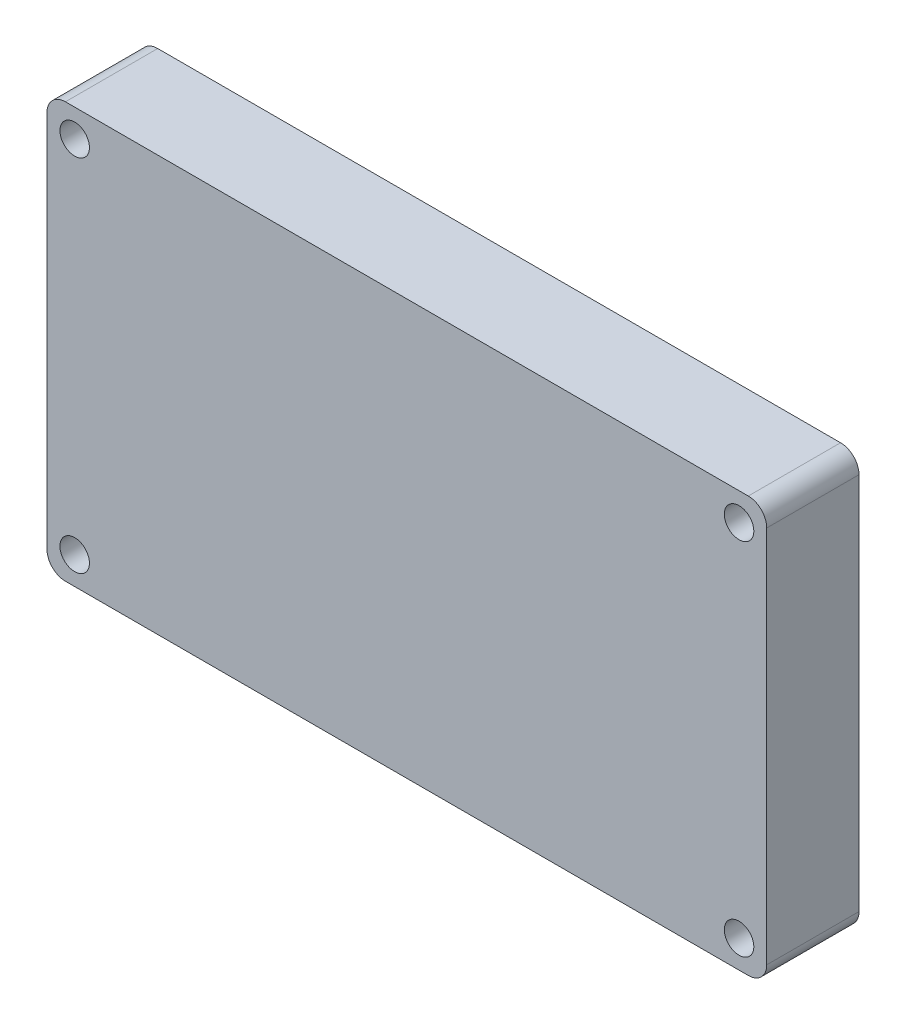
SolidWorks part; units mm, degrees
ref_plane "Front Plane" through (0, 0, 0) normal (0, 0, 1) x (1, 0, 0)
ref_plane "Top Plane" through (0, 0, 0) normal (0, 1, 0) x (1, 0, 0)
ref_plane "Right Plane" through (0, 0, 0) normal (1, 0, 0) x (0, 0, -1)
sketch "Sketch1" plane through (0, 0, 0) normal (0, 0, 1) x (1, 0, 0)
  line L0 (-78, 42) -> (-78, 43)
  line L1 (-3, 0) -> (-75, 0)
  line L2 (0, 3) -> (0, 42)
  line L3 (-3, 45) -> (-75, 45)
  line L4 (-78, 3) -> (-78, 42)
  line L5 (-76, 45) -> (-75, 45)
  line L6 (0, 42) -> (0, 43)
  line L7 (-2, 45) -> (-3, 45)
  line L8 (-3, 0) -> (-2, 0)
  line L9 (0, 2) -> (0, 3)
  line L10 (-75, 0) -> (-76, 0)
  line L11 (-78, 2) -> (-78, 3)
  circle A6 centre (-75, 3) radius 1.6
  circle A7 centre (-3, 3) radius 1.6
  circle A8 centre (-3, 42) radius 1.6
  arc A9 (0, 2) -> (-2, 0) centre (-2, 2) cw
  arc A10 (-2, 45) -> (0, 43) centre (-2, 43) cw
  arc A11 (-76, 45) -> (-78, 43) centre (-76, 43) ccw
  arc A12 (-76, 0) -> (-78, 2) centre (-76, 2) cw
  circle A14 centre (-75, 42) radius 1.6
  point P7 (0, 0)
  point P12 (-78, 0)
  point P15 (-78, 45)
  point P24 (0, 0)
  point P29 (-78, 45)
  point P32 (-78, 0)
  dimension "D3" = 2
  dimension "D4" = 3.2
  dimension "D5" = 3.2
  dimension "D6" = 3.2
  dimension "D1" = 78
  dimension "D2" = 45
extrude "Boss-Extrude2" add sketch "Sketch1" along normal blind 10
